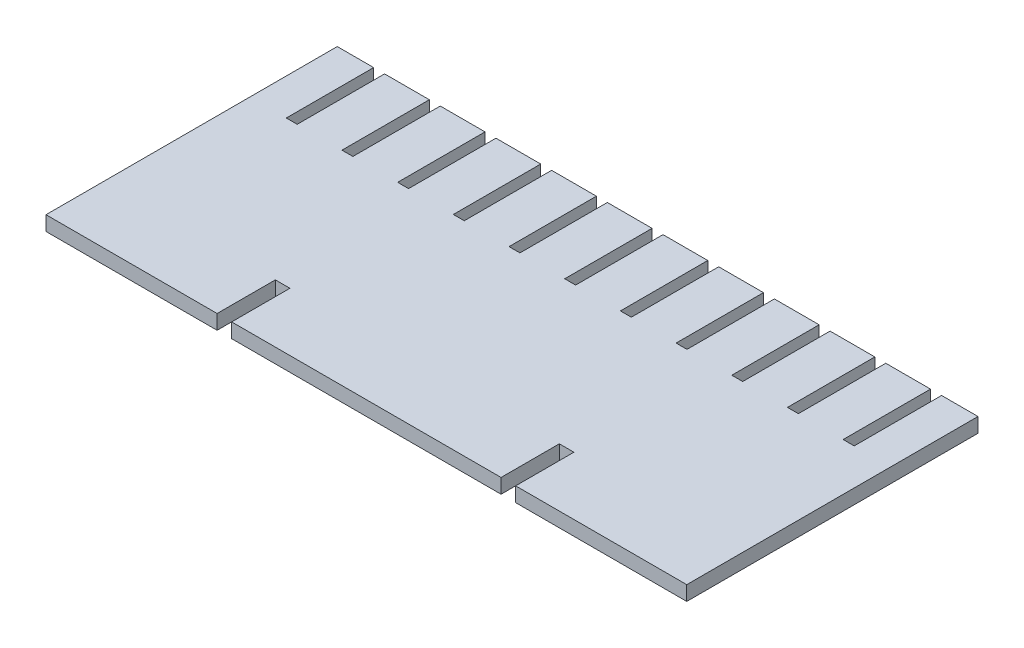
SolidWorks part; units mm, degrees
material "PE High Density"
ref_plane "Front Plane" through (0, 0, 0) normal (0, 0, 1) x (1, 0, 0)
ref_plane "Top Plane" through (0, 0, 0) normal (0, 1, 0) x (1, 0, 0)
ref_plane "Right Plane" through (0, 0, 0) normal (1, 0, 0) x (0, 0, -1)
sketch "Sketch1" plane through (0, 0, 0) normal (0, 1, 0) x (1, 0, 0)
  line L5 (0, 0) -> (0, 254)
  line L6 (0, 254) -> (31.75, 254)
  line L88 (31.75, 254) -> (31.75, 177.8)
  line L89 (31.75, 177.8) -> (41.275, 177.8)
  line L90 (41.275, 177.8) -> (41.275, 254)
  line L91 (0, 0) -> (149.225, 0)
  line L92 (149.225, 0) -> (149.225, 50.8)
  line L93 (149.225, 50.8) -> (161.925, 50.8)
  line L94 (161.925, 50.8) -> (161.925, 0)
  line L95 (41.275, 254) -> (80.3148, 254)
  line L96 (80.3148, 254) -> (80.3148, 177.8)
  line L97 (80.3148, 177.8) -> (89.8398, 177.8)
  line L98 (89.8398, 177.8) -> (89.8398, 254)
  line L99 (89.8398, 254) -> (128.8796, 254)
  line L100 (128.8796, 254) -> (128.8796, 177.8)
  line L101 (128.8796, 177.8) -> (138.4046, 177.8)
  line L102 (138.4046, 177.8) -> (138.4046, 254)
  line L103 (138.4046, 254) -> (177.4444, 254)
  line L104 (177.4444, 254) -> (177.4444, 177.8)
  line L105 (177.4444, 177.8) -> (186.9694, 177.8)
  line L106 (186.9694, 177.8) -> (186.9694, 254)
  line L107 (186.9694, 254) -> (226.0092, 254)
  line L108 (226.0092, 254) -> (226.0092, 177.8)
  line L109 (226.0092, 177.8) -> (235.5342, 177.8)
  line L110 (235.5342, 177.8) -> (235.5342, 254)
  line L111 (235.5342, 254) -> (274.574, 254)
  line L112 (274.574, 254) -> (274.574, 177.8)
  line L113 (274.574, 177.8) -> (284.099, 177.8)
  line L114 (284.099, 177.8) -> (284.099, 254)
  line L115 (284.099, 254) -> (323.1388, 254)
  line L116 (323.1388, 254) -> (323.1388, 177.8)
  line L117 (323.1388, 177.8) -> (332.6638, 177.8)
  line L118 (332.6638, 177.8) -> (332.6638, 254)
  line L119 (332.6638, 254) -> (371.7036, 254)
  line L120 (371.7036, 254) -> (371.7036, 177.8)
  line L121 (371.7036, 177.8) -> (381.2286, 177.8)
  line L122 (381.2286, 177.8) -> (381.2286, 254)
  line L123 (381.2286, 254) -> (420.2684, 254)
  line L124 (420.2684, 254) -> (420.2684, 177.8)
  line L125 (420.2684, 177.8) -> (429.7934, 177.8)
  line L126 (429.7934, 177.8) -> (429.7934, 254)
  line L127 (429.7934, 254) -> (468.8332, 254)
  line L128 (468.8332, 254) -> (468.8332, 177.8)
  line L129 (468.8332, 177.8) -> (478.3582, 177.8)
  line L130 (478.3582, 177.8) -> (478.3582, 254)
  line L131 (478.3582, 254) -> (517.398, 254)
  line L132 (517.398, 254) -> (517.398, 177.8)
  line L133 (517.398, 177.8) -> (527.05, 177.8)
  line L134 (527.05, 177.8) -> (527.05, 254)
  line L135 (527.05, 254) -> (558.8, 254)
  line L136 (558.8, 254) -> (558.8, 0)
  line L137 (558.8, 0) -> (409.575, 0)
  line L138 (409.575, 0) -> (409.575, 50.8)
  line L139 (409.575, 50.8) -> (396.875, 50.8)
  line L140 (396.875, 50.8) -> (396.875, 0)
  line L141 (396.875, 0) -> (161.925, 0)
  dimension "D1" = 9.525
  dimension "D2" = 12.7
  dimension "D3" = 127
  dimension "D4" = 127
  dimension "D5" = 558.8
  dimension "D6" = 9.652
  dimension "D7" = 149.225
  dimension "D8" = 76.2
  dimension "D10" = 31.75
  dimension "D9" = 10
  dimension "D11" = 149.225
  dimension "D12" = 12.7
  dimension "D13" = 254
  dimension "D14" = 31.75
extrude "Boss-Extrude1" add sketch "Sketch1" along normal blind 12.7
